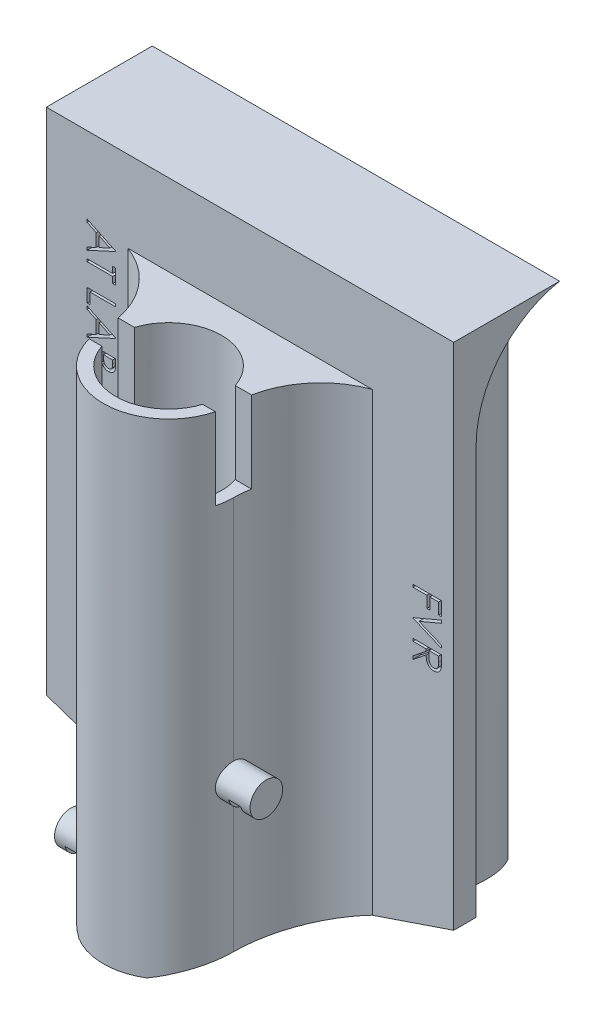
SolidWorks part; units mm, degrees
material "Pure Gold"
ref_plane "Alzado" through (0, 0, 0) normal (0, 0, 1) x (1, 0, 0)
ref_plane "Planta" through (0, 0, 0) normal (0, 1, 0) x (1, 0, 0)
ref_plane "Vista lateral" through (0, 0, 0) normal (1, 0, 0) x (0, 0, -1)
sketch "Sketch1" plane through (0, 0, 0) normal (0, 0, 1) x (1, 0, 0)
  line L0 (0, 0) -> (50, 0)
  line L1 (50, 0) -> (50, -62.5)
  line L2 (50, -62.5) -> (29.1725, -69.57)
  line L3 (29.1725, -69.57) -> (20.8275, -69.57)
  line L4 (20.8275, -69.57) -> (0, -62.5)
  line L5 (0, -62.5) -> (0, 0)
  point P8 (25, -69.57)
  point P9 (25, 0)
  dimension "D1" = 50
  dimension "D2" = 69.57
  dimension "D3" = 62.5
  dimension "D4" = 8.3449
extrude "Boss-Extrude1" add sketch "Sketch1" along normal blind 13
sketch "Sketch2" plane through (0, 0, 0) normal (0, 1, 0) x (1, 0, 0)
  line L0 (0, 0) -> (0, -10.25)
  line L1 (0, -10.25) -> (10.1637, -10.25)
  line L2 (0, -13) -> (0, 0) construction
  line L3 (0, 0) -> (6.3546, 0)
  line L4 (50, 0) -> (0, 0) construction
  line L5 (25, 0) -> (25, -17.3932) construction
  line L6 (50, -10.25) -> (39.8363, -10.25)
  line L7 (50, 0) -> (43.6454, 0)
  line L8 (50, 0) -> (50, -10.25)
  arc A5 (6.3546, 0) -> (10.1637, -10.25) centre (11.8246, -3.8) ccw
  arc A6 (43.6454, 0) -> (39.8363, -10.25) centre (38.1754, -3.8) cw
  dimension "D2" = 5.47
  dimension "D3" = 6.45
  dimension "D1" = 10.1637
  dimension "D4" = 10.25
extrude "Cut-Extrude1" cut sketch "Sketch2" against normal through all
sketch "Sketch3" plane through (0, 0, 0) normal (1, 0, 0) x (0, 0, -1)
  line L0 (-10.25, 0) -> (-10.25, -12.35)
  line L1 (-10.25, -62.5) -> (-10.25, 0) construction
  line L2 (-10.25, 0) -> (0, 0)
  arc A0 (0, 0) -> (-10.25, -12.35) centre (2.3151, -12.35) ccw
  dimension "D1" = 12.35
extrude "Boss-Extrude2" add sketch "Sketch3" along normal through all
sketch "Sketch4" plane through (0, 0, 0) normal (0, 1, 0) x (1, 0, 0)
  line L0 (10, -13) -> (10, -33)
  line L1 (50, -13) -> (0, -13) construction
  line L2 (10, -33) -> (40, -33)
  line L3 (40, -33) -> (40, -13)
  line L4 (40, -13) -> (10, -13)
  line L5 (0, -13) -> (0, 0) construction
  line L6 (50, -13) -> (50, 0) construction
  line L7 (25, -13) -> (25, -33) construction
  circle A0 centre (25, -23) radius 6.5
  dimension "D4" = 13
  dimension "D1" = 10
  dimension "D2" = 10
  dimension "D3" = 20
extrude "Boss-Extrude3" add sketch "Sketch4" against normal blind 20 from offset 50 offset against normal yes
sketch "Sketch5" plane through (0, -50, 0) normal (0, 1, 0) x (1, 0, 0)
  line L0 (10, -13) -> (40, -13)
  arc A0 (17, -23) -> (33, -23) centre (25, -23) ccw
  circle A1 centre (25, -23) radius 6.5
  arc A2 (10, -13) -> (17, -23) centre (6.3571, -23) cw
  arc A3 (40, -13) -> (33, -23) centre (43.6429, -23) ccw
  dimension "D1" = 13
  dimension "D2" = 16
extrude "Boss-Extrude4" add sketch "Sketch5" along normal blind 40
sketch "Sketch6" plane through (0, -10, 0) normal (0, 1, 0) x (1, 0, 0)
  line L0 (17, -23) -> (54.2857, -23) construction
  line L1 (16.8104, -21) -> (31.1847, -21)
  line L2 (17.254, -25) -> (31.1847, -25)
  line L3 (25, -16.5) -> (25, -29.5) construction
  arc A0 (40, -13) -> (33, -23) centre (43.6429, -23) ccw construction
  arc A1 (17, -23) -> (10, -13) centre (6.3571, -23) ccw construction
  circle A2 centre (25, -23) radius 6.5 construction
  arc A3 (17, -23) -> (33, -23) centre (25, -23) ccw construction
  arc A4 (31.1847, -21) -> (31.1847, -25) centre (37.3693, -23) ccw
  arc A5 (16.8104, -21) -> (17, -23) centre (6.3571, -23) cw
  arc A6 (17, -23) -> (17.254, -25) centre (25, -23) ccw
  dimension "D1" = 4
  dimension "D2" = 2
extrude "Cut-Extrude2" cut sketch "Sketch6" against normal blind 25
sketch "Sketch7" plane through (0, -10, 0) normal (0, 1, 0) x (1, 0, 0)
  line L0 (16.8104, -21) -> (33.1896, -21) construction
  line L1 (17.254, -25) -> (32.746, -25) construction
  line L2 (31.1847, -21) -> (33.1896, -21)
  line L3 (31.1847, -25) -> (32.746, -25)
  arc A0 (40, -13) -> (33, -23) centre (43.6429, -23) ccw construction
  arc A1 (17, -23) -> (33, -23) centre (25, -23) ccw construction
  circle A2 centre (25, -23) radius 6.5 construction
  arc A3 (31.1847, -21) -> (31.1847, -25) centre (25, -23) cw
  arc A4 (33.1896, -21) -> (33, -23) centre (43.6429, -23) ccw
  arc A5 (32.746, -25) -> (33, -23) centre (25, -23) ccw
extrude "Cut-Extrude3" cut sketch "Sketch7" against normal blind 10
sketch "Sketch9" plane through (0, -50, 0) normal (0, 1, 0) x (1, 0, 0)
  line L0 (10, -13) -> (10, -33)
  line L1 (10, -33) -> (40, -33)
  line L2 (40, -33) -> (40, -13)
  arc A0 (10, -13) -> (17, -23) centre (6.3571, -23) cw
  arc A1 (33, -23) -> (40, -13) centre (43.6429, -23) cw
  arc A2 (17, -23) -> (33, -23) centre (25, -23) ccw
  arc A3 (17.254, -25) -> (32.746, -25) centre (25, -23) ccw construction
  dimension "D1" = 8
extrude "Cut-Extrude6" cut sketch "Sketch9" against normal through all
sketch "Sketch10" plane through (0, 0, 13) normal (0, 0, 1) x (1, 0, 0)
  line L0 (40, -65.8945) -> (40, -70)
  line L1 (40, -70) -> (10, -70)
  line L2 (10, -70) -> (10, -65.8945)
  line L3 (10, -65.8945) -> (20.8275, -69.57)
  line L4 (20.8275, -69.57) -> (29.1725, -69.57)
  line L5 (29.1725, -69.57) -> (40, -65.8945)
extrude "Cut-Extrude7" cut sketch "Sketch10" along normal through all
ref_plane "Plane2" through (0, 0, 23) normal (0, 0, 1) x (1, 0, 0)
sketch "Sketch12" plane through (0, 0, 23) normal (0, 0, 1) x (1, 0, 0)
  line L0 (18, -65) -> (13, -65)
  line L1 (17, -35) -> (17, -68.2707) construction
  line L2 (13, -65) -> (13, -67)
  line L3 (13, -67) -> (18, -67)
  line L4 (18, -67) -> (18, -65)
  line L5 (4.5283, -65) -> (18, -65) construction
  dimension "D1" = 30
  dimension "D2" = 5
  dimension "D3" = 2
  dimension "D4" = 1
revolve "Revolve1" add sketch "Sketch12" angle 360 about L5
sketch "Sketch13" plane through (0, 0, 23) normal (0, 0, 1) x (1, 0, 0)
  line L0 (32, -50) -> (37, -50)
  line L2 (37, -50) -> (37, -52)
  line L3 (37, -52) -> (32, -52)
  line L4 (32, -52) -> (32, -50)
  line L5 (33, -20) -> (33, -68.2707) construction
  line L6 (32, -50) -> (52.0644, -50) construction
  dimension "D1" = 1
  dimension "D2" = 5
  dimension "D3" = 2
  dimension "D4" = 30
revolve "Revolve2" add sketch "Sketch13" angle 360 about L6
sketch "Sketch14" plane through (0, 0, 23) normal (0, 0, 1) x (1, 0, 0)
  line L0 (14.2, -67) -> (14.2, -65.5)
  line L1 (13, -67) -> (17, -67) construction
  line L2 (14.2, -65.5) -> (15.7, -65.5)
  line L3 (15.7, -65.5) -> (15.7, -67)
  line L4 (15.7, -67) -> (14.2, -67)
  line L5 (34.3, -52) -> (34.3, -50.5)
  line L6 (33, -52) -> (37, -52) construction
  line L7 (34.3, -50.5) -> (35.8, -50.5)
  line L8 (35.8, -50.5) -> (35.8, -52)
  line L9 (35.8, -52) -> (34.3, -52)
  line L10 (13, -63) -> (13, -67) construction
  line L11 (37, -52) -> (37, -48) construction
  dimension "D1" = 1.5
  dimension "D2" = 1.5
  dimension "D3" = 1.2
  dimension "D4" = 1.5
  dimension "D5" = 1.5
  dimension "D6" = 1.2
extrude "Cut-Extrude8" cut sketch "Sketch14" against normal up to next and the other way up to next
sketch "Sketch15" plane through (0, 0, 13) normal (0, 0, 1) x (1, 0, 0)
  line L0 (5, 0) -> (5, -64.1973) construction
  line L1 (0, 0) -> (0, -62.5) construction
  line L2 (45, 0) -> (45, -64.1973) construction
  line L3 (50, -62.5) -> (50, 0) construction
  line L4 (50, 0) -> (0, 0) construction
  text T0 "AT LAB DISP MED E2" font "Century Gothic" height 3.5
  text T1 "FVR"
  point P9 (5, -9.3689)
  point P10 (45, -64.1973)
  point P11 (45, 0)
  point P14 (5, 0)
  point P15 (5, -64.1973)
  dimension "D1" = 5
  dimension "D2" = 5
extrude "Cut-Extrude9" cut sketch "Sketch15" against normal blind 1
